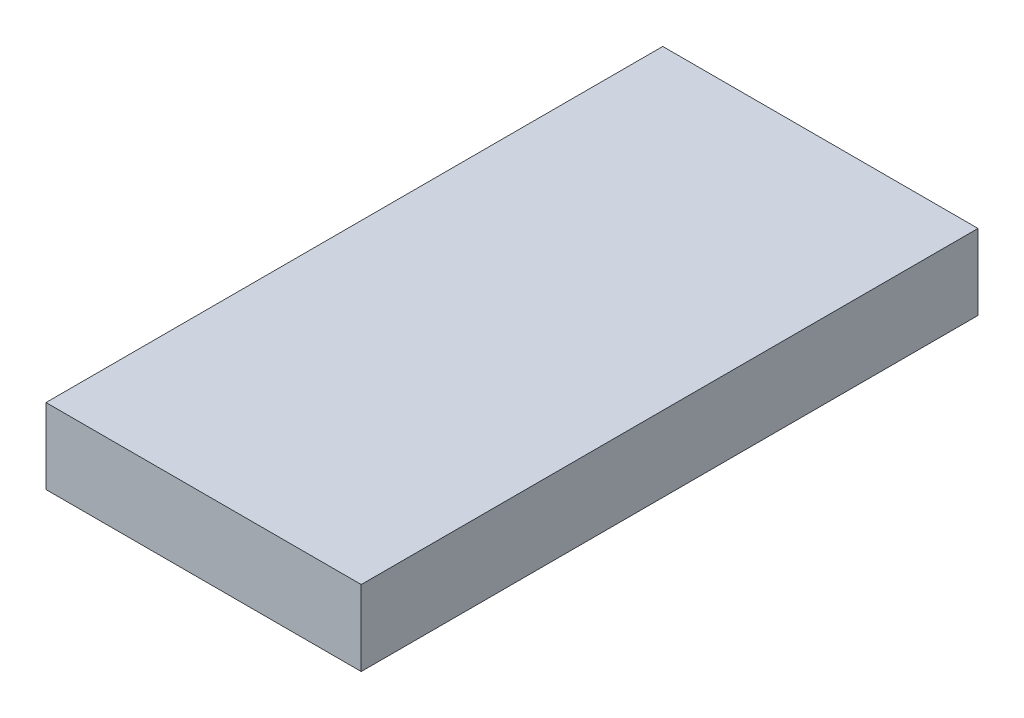
SolidWorks part; units mm, degrees
ref_plane "Front Plane" through (0, 0, 0) normal (0, 0, 1) x (1, 0, 0)
ref_plane "Top Plane" through (0, 0, 0) normal (0, 1, 0) x (1, 0, 0)
ref_plane "Right Plane" through (0, 0, 0) normal (1, 0, 0) x (0, 0, -1)
sketch "Sketch1" plane through (0, 0, 0) normal (0, 1, 0) x (1, 0, 0)
  line L1 (230, -450) -> (-230, -450)
  line L2 (230, -450) -> (230, 450)
  line L3 (230, 450) -> (-230, 450)
  line L4 (-230, -450) -> (-230, 450)
  line L5 (230, -450) -> (-230, 450) construction
  line L6 (230, 450) -> (-230, -450) construction
  point P0 (0, 0)
  dimension "D1" = 460
  dimension "D2" = 900
extrude "Boss-Extrude1" add sketch "Sketch1" along normal blind 110
